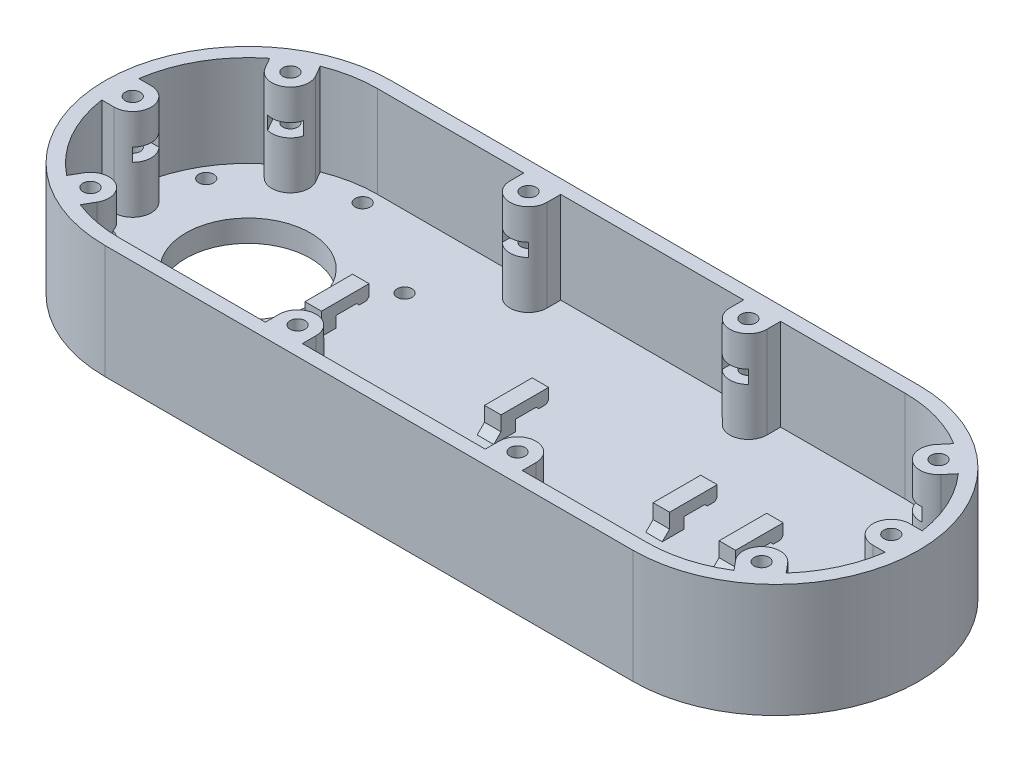
SolidWorks part; units mm, degrees
ref_plane "Front Plane" through (0, 0, 0) normal (0, 0, 1) x (1, 0, 0)
ref_plane "Top Plane" through (0, 0, 0) normal (0, 1, 0) x (1, 0, 0)
ref_plane "Right Plane" through (0, 0, 0) normal (1, 0, 0) x (0, 0, -1)
sketch "Sketch1" plane through (0, 0, 0) normal (0, 1, 0) x (1, 0, 0)
  line L0 (-144, 39) -> (0, 39)
  line L1 (-144, -39) -> (0, -39)
  arc A1 (-144, 39) -> (-144, -39) centre (-144, 0) ccw
  arc A3 (0, 39) -> (0, -39) centre (0, 0) cw
  dimension "D1" = 78
extrude "Boss-Extrude1" add sketch "Sketch1" along normal blind 6
sketch "Sketch2" plane through (0, 6, 0) normal (0, 1, 0) x (1, 0, 0)
  line L0 (-144, -35.25) -> (0, -35.25)
  line L1 (0, 35.25) -> (-144, 35.25)
  line L2 (-144, -39) -> (0, -39)
  line L3 (0, 39) -> (-144, 39)
  line L4 (-144, -39) -> (0, -39)
  line L5 (0, 39) -> (-144, 39)
  arc A0 (-144, 35.25) -> (-144, -35.25) centre (-144, 0) ccw
  arc A1 (0, -35.25) -> (0, 35.25) centre (0, 0) ccw
  arc A2 (-144, 39) -> (-144, -39) centre (-144, 0) ccw
  arc A4 (-144, 39) -> (-144, -39) centre (-144, 0) ccw
  arc A7 (0, -39) -> (0, 39) centre (0, 0) ccw construction
  arc A8 (0, -39) -> (0, 39) centre (0, 0) ccw
  arc A10 (0, -39) -> (0, 39) centre (0, 0) ccw
  dimension "D1" = 0
  dimension "D2" = 3.75
extrude "Boss-Extrude2" add sketch "Sketch2" along normal blind 25
sketch "Sketch3" plane through (0, 6, 0) normal (0, 1, 0) x (1, 0, 0)
  circle A0 centre (-144, 0) radius 17
  circle A2 centre (-144, 31.25) radius 2.05
  circle A3 centre (-116.9367, 15.625) radius 2.05
  circle A4 centre (-116.9367, -15.625) radius 2.05
  circle A5 centre (-144, -31.25) radius 2.05
  circle A6 centre (-171.0633, -15.625) radius 2.05
  circle A7 centre (-171.0633, 15.625) radius 2.05
  dimension "D1" = 34
  dimension "D3" = 4.1
  dimension "D2" = 31.25
  dimension "D4" = 6
extrude "Cut-Extrude1" cut sketch "Sketch3" against normal through all
sketch "Sketch4" plane through (0, 6, 0) normal (0, 1, 0) x (1, 0, 0)
  line L0 (-144, 0) -> (-175.5, 0) construction
  line L1 (-175.5, 5.05) -> (-178.8864, 5.05)
  line L2 (-175.5, -5.05) -> (-178.8864, -5.05)
  circle A0 centre (-175.5, 0) radius 2.05
  arc A1 (-175.5, -5.05) -> (-175.5, 5.05) centre (-175.5, 0) ccw
  arc A2 (-144, 35.25) -> (-144, -35.25) centre (-144, 0) ccw construction
  arc A3 (-178.8864, 5.05) -> (-178.8864, -5.05) centre (-144, 0) ccw
  circle A4 centre (-175.5, 0) radius 5.05 construction
  dimension "D1" = 4.1
  dimension "D2" = 31.5
  dimension "D3" = 3
extrude "Boss-Extrude3" add sketch "Sketch4" along normal up to surface (25 mm away) up to face at (-72, 31, 0)
ref_plane "Plane2" through (0, 19, 0) normal (0, 1, 0) x (1, 0, 0)
sketch "Sketch5" plane through (0, 19, 0) normal (0, 1, 0) x (1, 0, 0)
  line L1 (-171.9585, 3.6) -> (-177.5785, 3.6)
  line L2 (-177.5785, 3.6) -> (-179.6569, 0)
  line L3 (-179.6569, 0) -> (-177.5785, -3.6)
  line L4 (-177.5785, -3.6) -> (-171.9585, -3.6)
  line L7 (-173.4215, -3.6) -> (-172.3823, -1.8) [skipped]
  line L8 (-172.3823, 1.8) -> (-173.4215, 3.6) [skipped]
  circle A0 centre (-175.5, 0) radius 3.6 construction
  arc A1 (-175.5, -5.05) -> (-175.5, 5.05) centre (-175.5, 0) ccw construction
  arc A2 (-171.9585, -3.6) -> (-171.9585, 3.6) centre (-175.5, 0) ccw
  dimension "D1" = 7.2
extrude "Cut-Extrude2" cut sketch "Sketch5" along normal blind 3.6
pattern_circular "CirPattern2" count 2 every 60 about axis through (-144, 0, 0) along (0, 1, 0) of "Boss-Extrude3", "Cut-Extrude2"
sketch "Sketch6" plane through (0, 6, 0) normal (0, 1, 0) x (1, 0, 0)
  line L0 (0, 0) -> (31.5, 0) construction
  line L1 (31.5, 5.05) -> (34.8864, 5.05)
  line L2 (31.5, -5.05) -> (34.8864, -5.05)
  circle A0 centre (31.5, 0) radius 2.05
  arc A1 (31.5, 5.05) -> (31.5, -5.05) centre (31.5, 0) ccw
  arc A2 (0, -35.25) -> (0, 35.25) centre (0, 0) ccw construction
  arc A3 (0, -35.25) -> (34.8864, 5.05) centre (0, 0) ccw
  circle A4 centre (31.5, 0) radius 5.05 construction
  arc M23 (0, -35.25) -> (0, 35.25) centre (0, 0) ccw
  dimension "D2" = 4.1
  dimension "D1" = 31.5
  dimension "D3" = 3
extrude "Boss-Extrude4" add sketch "Sketch6" along normal up to surface (25 mm away) contours L1 A1 L2 A0 M23 up to face at (-72, 31, 0)
sketch "Sketch7" plane through (0, 19, 0) normal (0, 1, 0) x (1, 0, 0)
  line L1 (33.5785, 3.6) -> (27.9585, 3.6)
  line L4 (27.9585, -3.6) -> (33.5785, -3.6)
  line L5 (33.5785, -3.6) -> (35.6569, 0)
  line L6 (35.6569, 0) -> (33.5785, 3.6)
  line L7 (28.3823, 1.8) -> (27.3431, 0) [skipped]
  line L8 (28.3823, -1.8) -> (29.4215, -3.6) [skipped]
  circle A0 centre (31.5, 0) radius 3.6 construction
  arc A1 (31.5, 5.05) -> (31.5, -5.05) centre (31.5, 0) ccw construction
  arc A2 (27.9585, 3.6) -> (27.9585, -3.6) centre (31.5, 0) ccw
  dimension "D1" = 7.2
extrude "Cut-Extrude3" cut sketch "Sketch7" along normal blind 3.6
pattern_circular "CirPattern3" count 2 every 50 about axis through (0, 0, 0) along (0, 1, 0) of "Boss-Extrude4", "Cut-Extrude3"
sketch "Sketch8" plane through (0, 6, 0) normal (0, 1, 0) x (1, 0, 0)
  line L0 (0, 35.25) -> (-144, 35.25) construction
  line L1 (0, 35.25) -> (-144, 35.25)
  line L2 (-104.05, 31.5) -> (-104.05, 35.25)
  line L3 (-93.95, 31.5) -> (-93.95, 35.25)
  circle A0 centre (-99, 31.5) radius 2.05
  circle A1 centre (-144, 0) radius 17 construction
  arc A2 (-104.05, 31.5) -> (-93.95, 31.5) centre (-99, 31.5) ccw
  circle A3 centre (-99, 31.5) radius 5.05 construction
  dimension "D3" = 4.1
  dimension "D1" = 31.5
  dimension "D2" = 45
  dimension "D4" = 3
extrude "Boss-Extrude5" add sketch "Sketch8" along normal up to surface (25 mm away) contours L2 A2 L3 L1 A0 up to face at (-72, 31, 0)
sketch "Sketch9" plane through (0, 19, 0) normal (0, 1, 0) x (1, 0, 0)
  line L1 (-95.4, 33.5785) -> (-99, 35.6569)
  line L2 (-99, 35.6569) -> (-102.6, 33.5785)
  line L3 (-102.6, 33.5785) -> (-102.6, 27.9585)
  line L6 (-95.4, 27.9585) -> (-95.4, 33.5785)
  line L7 (-99, 27.3431) -> (-97.2, 28.3823) [skipped]
  line L8 (-102.6, 29.4215) -> (-100.8, 28.3823) [skipped]
  circle A0 centre (-99, 31.5) radius 3.6 construction
  arc A1 (-104.05, 31.5) -> (-93.95, 31.5) centre (-99, 31.5) ccw construction
  arc A2 (-102.6, 27.9585) -> (-95.4, 27.9585) centre (-99, 31.5) ccw
  dimension "D1" = 7.2
extrude "Cut-Extrude4" cut sketch "Sketch9" along normal blind 3.6
pattern_linear "LPattern1" count 2 spacing 60 along (1, 0, 0) of "Cut-Extrude4", "Boss-Extrude5"
mirror "Mirror2" about plane through (0, 0, 0) normal (0, 0, 1) of "LPattern1", "Cut-Extrude4", "Boss-Extrude5"
ref_plane "Plane4" through (-5, 0, 0) normal (1, 0, 0) x (0, 0, -1)
sketch "Sketch10" plane through (-5, 0, 0) normal (1, 0, 0) x (0, 0, -1)
  line L0 (-2, 6) -> (-2, 9)
  line L1 (17, 6) -> (-17, 6) construction
  line L2 (-2, 9) -> (3.6049, 9)
  line L3 (3.6049, 9) -> (4.3025, 8.3025)
  line L4 (4.3025, 8.3025) -> (6.3025, 8.3025)
  line L5 (6.3025, 8.3025) -> (7, 9)
  line L6 (7, 9) -> (7, 12)
  line L7 (7, 12) -> (-6, 12)
  line L8 (-6, 12) -> (-6, 6)
  line L9 (-13.575, 6) -> (-17.675, 6) construction
  line L10 (-39, 31) -> (-39, 0) construction
  line L11 (5.05, 6) -> (-5.05, 6) construction
  line L12 (-6, 6) -> (-2, 6)
  dimension "D1" = 33
  dimension "D2" = 4
  dimension "D3" = 3
  dimension "D4" = 3
  dimension "D5" = 0.6975
  dimension "D6" = 135
  dimension "D7" = 3
  dimension "D8" = 2
  dimension "D9" = 13
extrude "Boss-Extrude6" add sketch "Sketch10" against normal blind 4.5
pattern_linear "LPattern2" count 2 spacing 18 along (-1, 0, 0) of "Boss-Extrude6"
pattern_linear "LPattern3" count 2 spacing 64 along (-1, 0, 0) of "Boss-Extrude6"
pattern_linear "LPattern4" count 2 spacing 113 along (-1, 0, 0) of "Boss-Extrude6"
chamfer "Chamfer1" distance 2 angle 45 4 edges at (-7.25, 6, 6) (-25.25, 6, 6) (-71.25, 6, 6) (-120.25, 6, 6)
